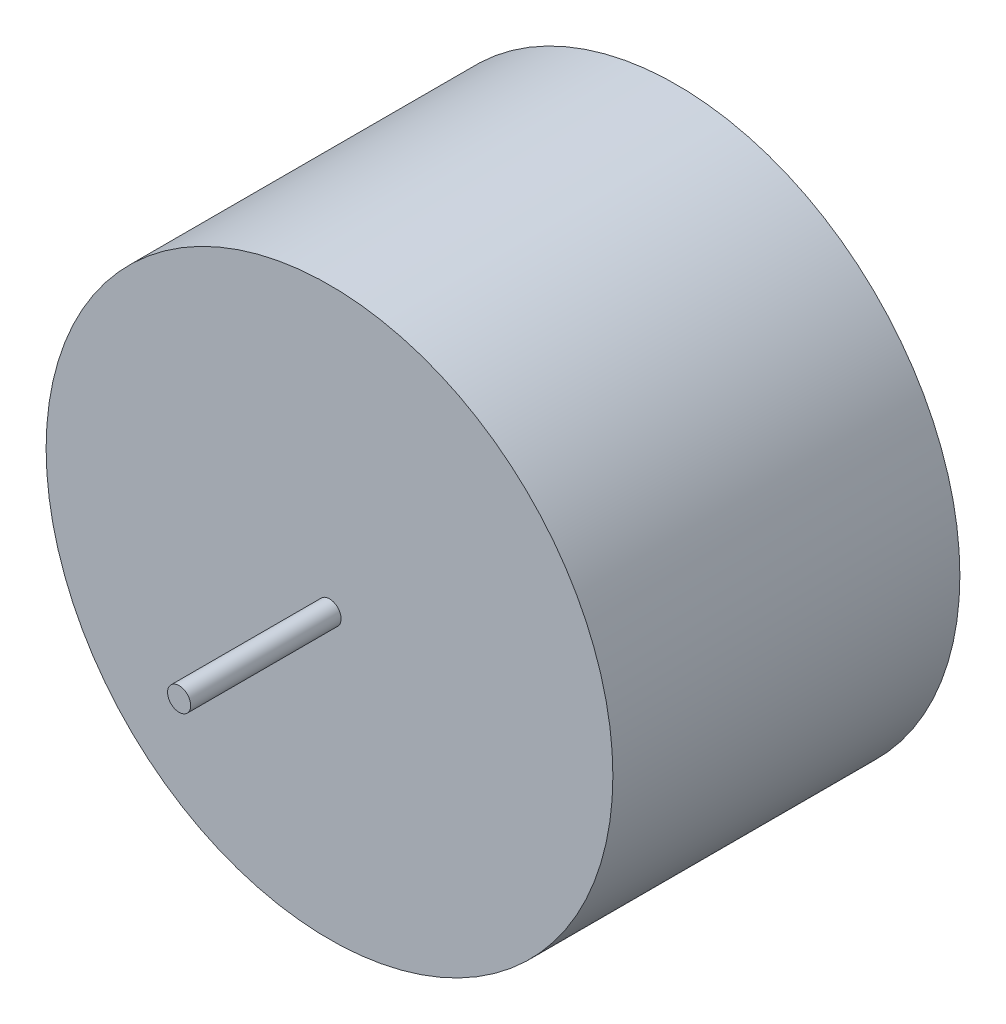
SolidWorks part; units mm, degrees
ref_plane "Alzado" through (0, 0, 0) normal (0, 0, 1) x (1, 0, 0)
ref_plane "Planta" through (0, 0, 0) normal (0, 1, 0) x (1, 0, 0)
ref_plane "Vista lateral" through (0, 0, 0) normal (1, 0, 0) x (0, 0, -1)
sketch "Croquis1" plane through (0, 0, 0) normal (0, 0, 1) x (1, 0, 0)
  circle A0 centre (0, 0) radius 85.75
  dimension "D1" = 171.5
extrude "Saliente-Extruir1" add sketch "Croquis1" along normal blind 105
sketch "Croquis2" plane through (0, 0, 0) normal (0, 0, 1) x (1, 0, 0)
  circle A0 centre (0, 0) radius 21
  dimension "D1" = 42
extrude "Saliente-Extruir2" add sketch "Croquis2" against normal blind 10.5
sketch "Croquis3" plane through (0, 0, 0) normal (0, 0, -1) x (-1, 0, 0)
  circle A0 centre (0, 0) radius 3.5
  dimension "D1" = 7
extrude "Saliente-Extruir4" add sketch "Croquis3" against normal blind 150.5
